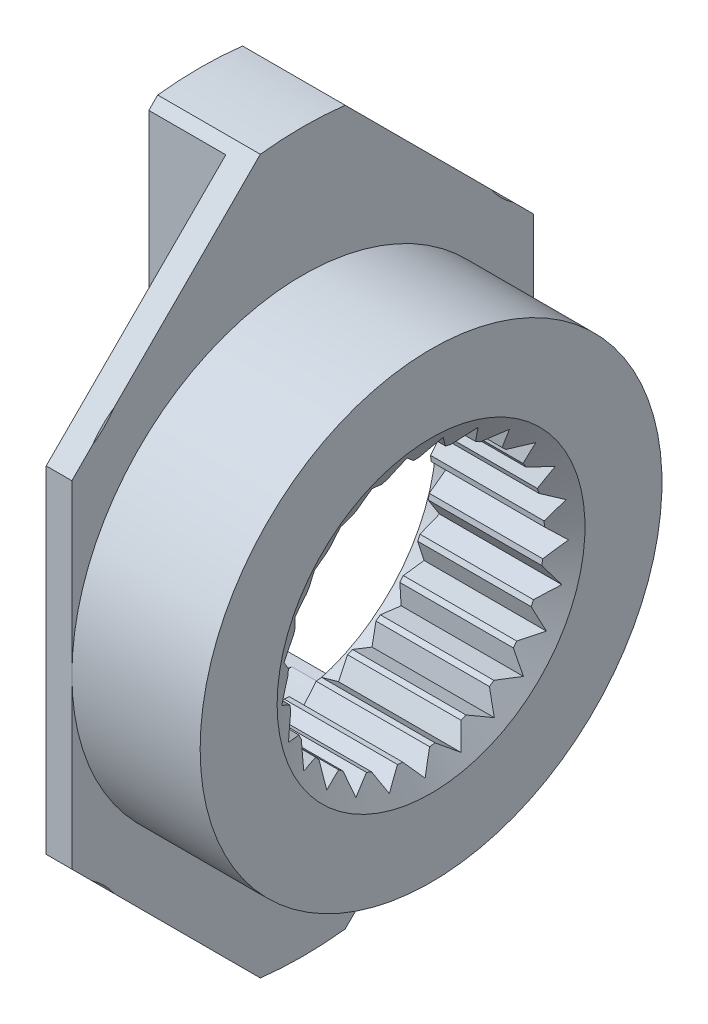
SolidWorks part; units mm, degrees
ref_plane "Спереди" through (0, 0, 0) normal (0, 0, 1) x (1, 0, 0)
ref_plane "Сверху" through (0, 0, 0) normal (0, 1, 0) x (1, 0, 0)
ref_plane "Справа" through (0, 0, 0) normal (1, 0, 0) x (0, 0, -1)
sketch "Эскиз1" plane through (0, 0, 0) normal (0, 0, 1) x (1, 0, 0)
  line L0 (0, 0) -> (19.4097, 0) construction
  line L1 (0, 1.5) -> (0, 10)
  line L2 (0, 10) -> (2, 10)
  line L3 (2, 10) -> (2, 4.5)
  line L4 (2, 4.5) -> (4.5, 4.5)
  line L5 (4.5, 4.5) -> (4.5, 2.5)
  line L6 (4.5, 2.5) -> (2, 2.5)
  line L7 (1, 3.1) -> (1, 1.5)
  line L8 (1, 1.5) -> (0, 1.5)
  line L9 (2, 2.5) -> (2, 3.1)
  line L10 (2, 3.1) -> (1, 3.1)
  dimension "D1" = 20
  dimension "D2" = 3
  dimension "D3" = 5
  dimension "D4" = 9
  dimension "D5" = 4.5
  dimension "D6" = 2
  dimension "D7" = 3.5
  dimension "D8" = 6.2
  dimension "D9" = 1
revolve "Повернуть1" add sketch "Эскиз1" angle 360 about L0
chamfer "Фаска1" distance 0.5 angle 30 1 edges at (4.5, 0, 2.5)
sketch "Эскиз3" plane through (4.5, 0, 0) normal (1, 0, 0) x (0, 0, -1)
  line L0 (0, 2.45) -> (0, 0) construction
  line L1 (0, 0) -> (0.6093, 2.373) construction
  line L2 (0, 2.45) -> (0.3509, 2.7779)
  line L3 (0.3509, 2.7779) -> (0.6093, 2.373)
  line L4 (0.3509, 2.7779) -> (0, 0) construction
  line L5 (0.6093, 2.373) -> (1.0307, 2.6034)
  line L6 (1.0307, 2.6034) -> (1.1803, 2.147)
  line L7 (1.1803, 2.147) -> (1.6458, 2.2652)
  line L8 (1.6458, 2.2652) -> (1.6771, 1.786)
  line L9 (1.6771, 1.786) -> (2.1574, 1.7848)
  line L10 (2.1574, 1.7848) -> (2.0686, 1.3128)
  line L11 (2.0686, 1.3128) -> (2.5335, 1.1922)
  line L12 (2.5335, 1.1922) -> (2.3301, 0.7571)
  line L13 (2.3301, 0.7571) -> (2.7504, 0.5247)
  line L14 (2.7504, 0.5247) -> (2.4452, 0.1538)
  line L15 (2.4452, 0.1538) -> (2.7945, -0.1758)
  line L16 (2.7945, -0.1758) -> (2.4066, -0.4591)
  line L17 (2.4066, -0.4591) -> (2.663, -0.8652)
  line L18 (2.663, -0.8652) -> (2.2168, -1.0432)
  line L19 (2.2168, -1.0432) -> (2.3641, -1.5003)
  line L20 (2.3641, -1.5003) -> (1.8878, -1.5617)
  line L21 (1.8878, -1.5617) -> (1.9167, -2.0411)
  line L22 (1.9167, -2.0411) -> (1.4401, -1.9821)
  line L23 (1.4401, -1.9821) -> (1.3489, -2.4537)
  line L24 (1.3489, -2.4537) -> (0.9019, -2.278)
  line L25 (0.9019, -2.278) -> (0.6963, -2.712)
  line L26 (0.6963, -2.712) -> (0.3071, -2.4307)
  line L27 (0.3071, -2.4307) -> (0, -2.8)
  line L28 (0, -2.8) -> (-0.3071, -2.4307)
  line L29 (-0.3071, -2.4307) -> (-0.6963, -2.712)
  line L30 (-0.6963, -2.712) -> (-0.9019, -2.278)
  line L31 (-0.9019, -2.278) -> (-1.3489, -2.4537)
  line L32 (-1.3489, -2.4537) -> (-1.4401, -1.9821)
  line L33 (-1.4401, -1.9821) -> (-1.9167, -2.0411)
  line L34 (-1.9167, -2.0411) -> (-1.8878, -1.5617)
  line L35 (-1.8878, -1.5617) -> (-2.3641, -1.5003)
  line L36 (-2.3641, -1.5003) -> (-2.2168, -1.0432)
  line L37 (-2.2168, -1.0432) -> (-2.663, -0.8652)
  line L38 (-2.663, -0.8652) -> (-2.4066, -0.4591)
  line L39 (-2.4066, -0.4591) -> (-2.7945, -0.1758)
  line L40 (-2.7945, -0.1758) -> (-2.4452, 0.1538)
  line L41 (-2.4452, 0.1538) -> (-2.7504, 0.5247)
  line L42 (-2.7504, 0.5247) -> (-2.3301, 0.7571)
  line L43 (-2.3301, 0.7571) -> (-2.5335, 1.1922)
  line L44 (-2.5335, 1.1922) -> (-2.0686, 1.3128)
  line L45 (-2.0686, 1.3128) -> (-2.1574, 1.7848)
  line L46 (-2.1574, 1.7848) -> (-1.6771, 1.786)
  line L47 (-1.6771, 1.786) -> (-1.6458, 2.2652)
  line L48 (-1.6458, 2.2652) -> (-1.1803, 2.147)
  line L49 (-1.1803, 2.147) -> (-1.0307, 2.6034)
  line L50 (-1.0307, 2.6034) -> (-0.6093, 2.373)
  line L51 (-0.6093, 2.373) -> (-0.3509, 2.7779)
  line L52 (-0.3509, 2.7779) -> (0, 2.45)
  circle A0 centre (0, 0) radius 2.45 construction
  circle A1 centre (0, 0) radius 2.8 construction
  dimension "D4" = 4.9
  dimension "D5" = 5.6
  dimension "D1" = 14.4
  dimension "D2" = 7.2
  dimension "D3" = 25
extrude "Вырез-Вытянуть1" cut sketch "Эскиз3" against normal up to surface (2.5 mm away) up to face at (2, 0, 2.5)
hole_wizard "Отверстие обработанное метчиком M3x0.51" positions "Эскиз5" profile "Эскиз6" tap size "M3x0.5" standard "Ansi (метрические)" end condition up to next
sketch "Эскиз5" plane through (0, 0, 0) normal (-1, 0, 0) x (0, 0, 1)
  circle A0 centre (0, 0) radius 1.5 construction
  point P0 (-5, 5)
  point P1 (5, 5)
  point P3 (5, -5)
  point P5 (-5, -5)
  dimension "D4" = 5
  dimension "D1" = 10
  dimension "D2" = 10
  dimension "D3" = 5
sketch "Эскиз6" plane through (0, 5, -5) normal (0, 1, 0) x (0, 0, 1)
  line L0 (0, 0) -> (0, 2)
  line L1 (0, 2) -> (1.6, 2)
  line L2 (1.25, 1.7549) -> (1.25, 0.2451)
  line L3 (1.25, 0.2451) -> (1.6, 0)
  line L5 (1.6, 0) -> (0, 0)
  line L6 (-1.25, 0.2451) -> (-1.6, 0) construction
  line L7 (1.6, 2) -> (1.25, 1.7549)
  line L8 (-1.6, 2) -> (-1.25, 1.7549) construction
  line L11 (0, -6.35) -> (0, 107.95) construction
  dimension "Диаметр резьбы" = 2.5
  dimension "Глубина проходного сверла" = 2
  dimension "Диаметр передней зенковки" = 3.2
  dimension "Угол передней зенковки" = 110
  dimension "Диаметр задней зенковки" = 3.2
  dimension "Угол задней зенковки" = 110
sketch "Эскиз7" plane through (0, 0, 0) normal (0, 0, 1) x (1, 0, 0)
  line L0 (0, 0) -> (4.5, 0) construction
  line L1 (4.5, -4.5) -> (4.5, 4.5) construction
  line L2 (0, 7) -> (2, 7)
  line L3 (0, 10) -> (0, -10) construction
  line L4 (2, -10) -> (2, 10) construction
  line L5 (0, 7) -> (0, 10)
  line L6 (0, 10) -> (2, 10)
  line L7 (2, 10) -> (2, 7)
  dimension "D1" = 14
revolve "Вырез-Повернуть1" cut sketch "Эскиз7" angle 360 about L0
sketch "Эскиз8" plane through (0, 0, 0) normal (-1, 0, 0) x (0, 0, 1)
  line L0 (-0.8272, 6.9509) -> (-4.5, 3.2782)
  line L1 (-4.5, 3.2782) -> (-4.5, -3.2782)
  line L2 (-4.5, -3.2782) -> (-0.8272, -6.9509)
  line L3 (0.8272, 6.9509) -> (4.5, 3.2782)
  line L4 (4.5, 3.2782) -> (4.5, -3.2782)
  line L5 (4.5, -3.2782) -> (0.8272, -6.9509)
  line L6 (-0.8272, 6.9509) -> (-0.8272, 9.0493)
  line L7 (-0.8272, 9.0493) -> (0.8272, 9.0493)
  line L8 (0.8272, 9.0493) -> (0.8272, 6.9509)
  line L9 (-0.8272, -6.9509) -> (-0.8272, -8.3012)
  line L10 (-0.8272, -8.3012) -> (0.8272, -8.3012)
  line L11 (0.8272, -8.3012) -> (0.8272, -6.9509)
  arc A0 (3.7047, 5.9393) -> (-3.7047, 5.9393) centre (0, 0) ccw construction
  arc A1 (-3.7047, -5.9393) -> (3.7047, -5.9393) centre (0, 0) ccw construction
  circle A2 centre (0, 0) radius 1.5 construction
  dimension "D1" = 5.5
  dimension "D3" = 5.5
  dimension "D2" = 9
extrude "Вырез-Вытянуть2" cut sketch "Эскиз8" against normal blind 2.2 flip side to cut
sketch "Эскиз9" plane through (0, 0, -4.5) normal (0, 0, -1) x (-1, 0, 0)
  line L0 (0, 3) -> (-1.5, 3)
  line L2 (-1.5, 3) -> (-1.5, -3)
  line L3 (-1.5, -3) -> (0, -3)
  line L4 (0, -3) -> (0, 3)
  dimension "D1" = 3
  dimension "D2" = 6
  dimension "D3" = 1.5
extrude "Вырез-Вытянуть3" cut sketch "Эскиз9" against normal through all
sketch "Эскиз10" plane through (0, 0, 0) normal (0, 1, 0) x (1, 0, 0)
  line L0 (1.5, 1) -> (1.5, 5.5129)
  line L1 (1.5, 0.781) -> (1.5, 4.5) construction
  line L2 (1.5, 5.5129) -> (-0.6067, 5.5129)
  line L3 (-0.6067, 5.5129) -> (-0.6067, -5.0784)
  line L4 (-0.6067, -5.0784) -> (1.5, -5.0784)
  line L5 (1.5, -5.0784) -> (1.5, -1)
  line L6 (1.5, -4.5) -> (1.5, -0.781) construction
  line L7 (1.5, -1) -> (0, -1)
  line L8 (0, -1) -> (0, 1)
  line L9 (0, 1) -> (1.5, 1)
  dimension "D1" = 2
extrude "Вырез-Вытянуть4" cut sketch "Эскиз10" against normal through all and the other way through all contours L8 L9 L0 L2 L3 L4 L5 L7
